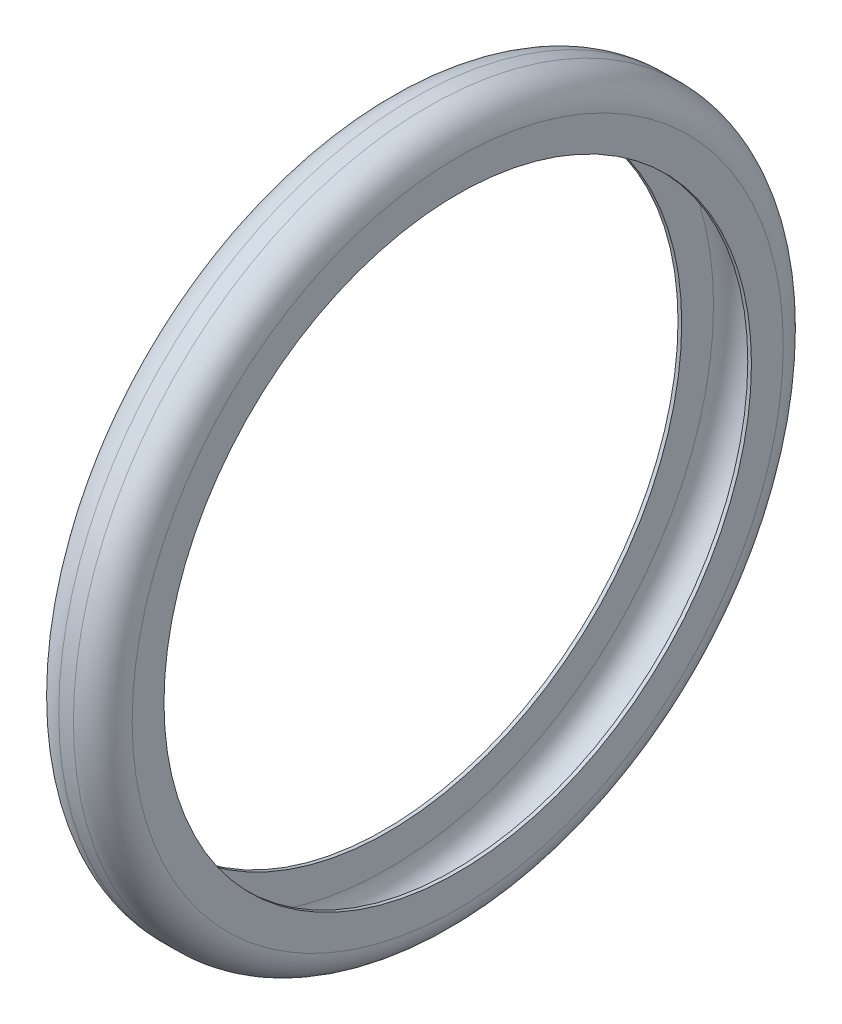
SolidWorks part; units mm, degrees
ref_plane "Front Plane" through (0, 0, 0) normal (0, 0, 1) x (1, 0, 0)
ref_plane "Top Plane" through (0, 0, 0) normal (0, 1, 0) x (1, 0, 0)
ref_plane "Right Plane" through (0, 0, 0) normal (1, 0, 0) x (0, 0, -1)
sketch "Sketch1" plane through (29.8207, 0, 0) normal (0, -0.5871, 0.8095) x (1, 0, 0)
sketch "Sketch3" plane through (0, 0, 0) normal (1, 0, 0) x (0, 0, -1)
  circle A0 centre (0, 0) radius 240
  circle A1 centre (0, 0) radius 290
  dimension "D1" = 480
  dimension "D2" = 580
extrude "Boss-Extrude1" add sketch "Sketch3" along normal blind 60
fillet "Fillet1" radius 24 2 edges at (0, 0, -290) (60, 0, -290)
shell "Shell1" thickness 3
